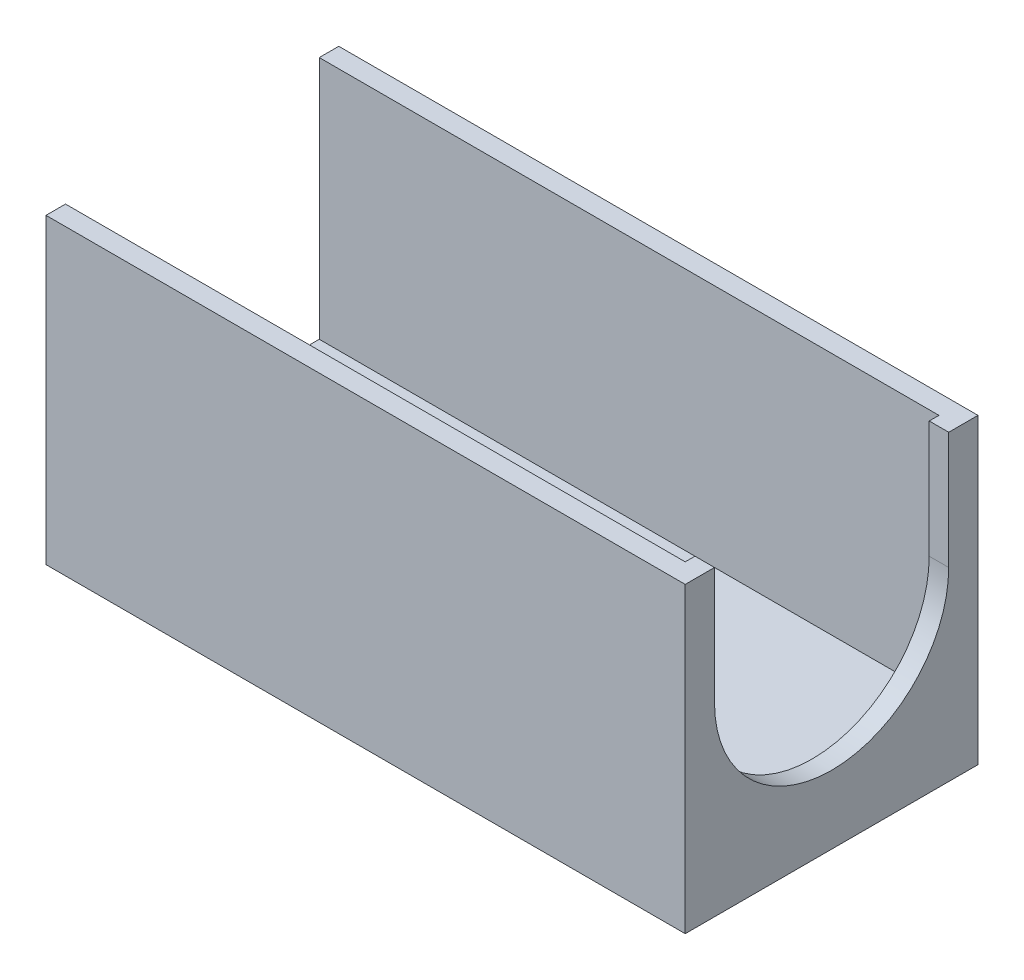
SolidWorks part; units mm, degrees
ref_plane "Front Plane" through (0, 0, 0) normal (0, 0, 1) x (1, 0, 0)
ref_plane "Top Plane" through (0, 0, 0) normal (0, 1, 0) x (1, 0, 0)
ref_plane "Right Plane" through (0, 0, 0) normal (1, 0, 0) x (0, 0, -1)
sketch "Sketch1" plane through (0, 0, 0) normal (0, 1, 0) x (1, 0, 0)
  line L1 (-33, -15) -> (33, -15)
  line L2 (-33, -15) -> (-33, 15)
  line L3 (-33, 15) -> (33, 15)
  line L4 (33, -15) -> (33, 15)
  line L5 (-33, -15) -> (33, 15) construction
  line L6 (-33, 15) -> (33, -15) construction
  point P0 (0, 0)
  dimension "D1" = 66
  dimension "D2" = 30
extrude "Boss-Extrude1" add sketch "Sketch1" along normal blind 31
sketch "Sketch2" plane through (0, 31, 0) normal (0, 1, 0) x (1, 0, 0)
  line L0 (-33, 15) -> (-33, -15) construction
  line L1 (-33, 13) -> (31, 13)
  line L2 (-33, 13) -> (-33, -13)
  line L3 (-33, -13) -> (31, -13)
  line L4 (31, 13) -> (31, -13)
  line L5 (33, 15) -> (-33, 15) construction
  line L6 (-33, -15) -> (33, -15) construction
  line L7 (33, -15) -> (33, 15) construction
  dimension "D1" = 2
  dimension "D2" = 2
  dimension "D3" = 2
extrude "Cut-Extrude1" cut sketch "Sketch2" against normal blind 25
sketch "Sketch3" plane through (0, 0, 15) normal (0, 0, 1) x (1, 0, 0)
  line L0 (-33, 31) -> (-33, 0) construction
  line L1 (-33, 0) -> (33, 0) construction
  line L3 (-36, 0) -> (-33, 0)
  line L4 (-36, 0) -> (-36, 3.2796)
  line L5 (-36, 6) -> (-33, 6)
  line L6 (-33, 0) -> (-33, 6)
  arc A0 (-36, 6) -> (-36, 0) centre (-36, 3) ccw
  circle A1 centre (-36, 3) radius 1
  dimension "D1" = 6
  dimension "D4" = 2
  dimension "D2" = 3
  dimension "D3" = 3
extrude "Boss-Extrude2" add sketch "Sketch3" against normal blind 30
sketch "Sketch4" plane through (0, 0, 15) normal (0, 0, 1) x (1, 0, 0)
  line L1 (-33, 6) -> (-39, 6)
  line L2 (-33, 6) -> (-33, 0)
  line L3 (-33, 0) -> (-39, 0)
  line L4 (-39, 6) -> (-39, 0)
  dimension "D1" = 6
  dimension "D2" = 6
extrude "Cut-Extrude2" cut sketch "Sketch4" against normal blind 8.25
sketch "Sketch5" plane through (0, 0, -15) normal (0, 0, -1) x (-1, 0, 0)
  line L1 (33, 6) -> (39, 6)
  line L2 (33, 6) -> (33, 0)
  line L3 (33, 0) -> (39, 0)
  line L4 (39, 6) -> (39, 0)
  dimension "D1" = 6
  dimension "D2" = 6
extrude "Cut-Extrude3" cut sketch "Sketch5" against normal blind 8.25
sketch "Sketch6" plane through (0, 0, 0) normal (0, -1, 0) x (1, 0, 0)
  line L1 (-33, -15) -> (-32.5, -15)
  line L2 (-33, -15) -> (-33, -6.75)
  line L3 (-33, -6.75) -> (-32.5, -6.75)
  line L4 (-32.5, -15) -> (-32.5, -6.75)
  line L5 (-33, 15) -> (-32.5, 15)
  line L6 (-33, 15) -> (-33, 6.75)
  line L7 (-33, 6.75) -> (-32.5, 6.75)
  line L8 (-32.5, 15) -> (-32.5, 6.75)
  point P10 (-32.75, -6.75)
  dimension "D1" = 0.5
  dimension "D2" = 8.25
  dimension "D3" = 8.25
  dimension "D4" = 0.5
extrude "Cut-Extrude4" cut sketch "Sketch6" against normal blind 31
sketch "Sketch7" plane through (33, 0, 0) normal (1, 0, 0) x (0, 0, -1)
  line L0 (-15, 31) -> (15, 31) construction
  line L1 (-15, 31) -> (-15, 0) construction
  line L3 (12, 19) -> (12, 31)
  line L4 (12, 31) -> (-12, 31)
  line L5 (-12, 19) -> (-12, 31)
  arc A0 (-12, 19) -> (12, 19) centre (0, 19) ccw
  dimension "D1" = 24
  dimension "D2" = 12
  dimension "D3" = 15
  dimension "D4" = 24
extrude "Cut-Extrude5" cut sketch "Sketch7" against normal blind 2
